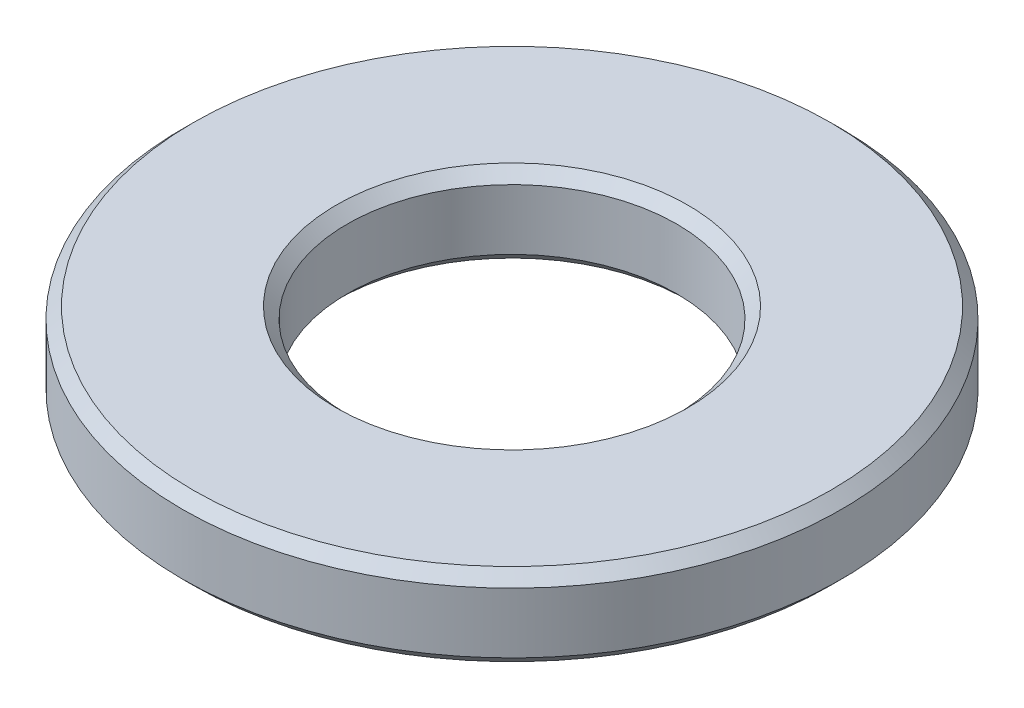
SolidWorks part; units mm, degrees
ref_plane "前视基准面" through (0, 0, 0) normal (0, 0, 1) x (1, 0, 0)
ref_plane "上视基准面" through (0, 0, 0) normal (0, 1, 0) x (1, 0, 0)
ref_plane "右视基准面" through (0, 0, 0) normal (1, 0, 0) x (0, 0, -1)
sketch "草图1" plane through (0, 0, 0) normal (0, 1, 0) x (1, 0, 0)
  circle A0 centre (0, 0) radius 6
  circle A1 centre (0, 0) radius 3
  dimension "D1" = 6
  dimension "D2" = 12
extrude "凸台-拉伸1" add sketch "草图1" along normal blind 1.5
chamfer "倒角1" distance 0.2 angle 45 4 edges at (0, 0, 3) (0, 0, 6) (0, 1.5, 6) (0, 1.5, 3)
